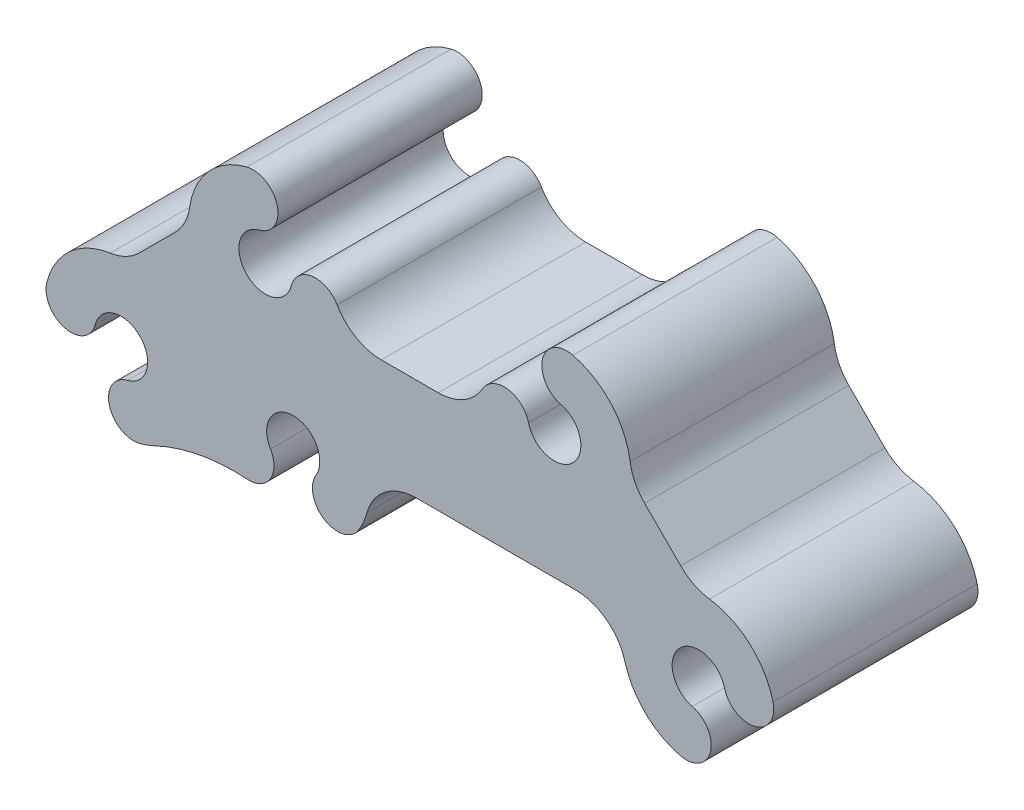
SolidWorks part; units mm, degrees
ref_plane "Front Plane" through (0, 0, 0) normal (0, 0, 1) x (1, 0, 0)
ref_plane "Top Plane" through (0, 0, 0) normal (0, 1, 0) x (1, 0, 0)
ref_plane "Right Plane" through (0, 0, 0) normal (1, 0, 0) x (0, 0, -1)
ref_plane "Plane1" through (0, 0, 0) normal (0, 0, -1) x (-1, 0, 0)
sketch "Sketch1" plane through (0, 0, 0) normal (0, 0, -1) x (-1, 0, 0)
  line L0 (-28.4032, 13.6299) -> (-32.8933, 9.1398)
  line L1 (-19.8469, 0) -> (0, 0)
  line L2 (34.4586, 9.1398) -> (29.9685, 13.6299)
  line L3 (4.3259, 12.7) -> (-2.7576, 12.7)
  arc A0 (-26.6071, 17.222) -> (-28.4032, 13.6299) centre (-32.8933, 18.1201) cw
  arc A1 (-32.8933, 9.1398) -> (-36.4854, 7.3438) centre (-37.3834, 13.6299) cw
  arc A2 (-36.4854, 7.3438) -> (-44.3795, 0.2224) centre (-35.1384, -2.0855) ccw
  arc A3 (-44.3795, 0.2224) -> (-38.342, -1.2854) centre (-41.3607, -0.5315) ccw
  arc A4 (-38.342, -1.2854) -> (-34.3383, -5.2891) centre (-35.1384, -2.0855) cw
  arc A5 (-34.3383, -5.2891) -> (-32.8305, -11.3267) centre (-33.5844, -8.3079) ccw
  arc A6 (-32.8305, -11.3267) -> (-25.9635, -4.6442) centre (-35.1384, -2.0855) ccw
  arc A7 (-25.9635, -4.6442) -> (-19.8469, 0) centre (-19.8469, -6.35) cw
  arc A8 (0, 0) -> (6.1166, -4.6442) centre (0, -6.35) cw
  arc A9 (6.1166, -4.6442) -> (7.1251, -6.9881) centre (15.2915, -2.0855) ccw
  arc A10 (7.1251, -6.9881) -> (12.4605, -3.7851) centre (9.7928, -5.3866) ccw
  arc A11 (12.4605, -3.7851) -> (18.1225, -3.7851) centre (15.2915, -2.0855) cw
  arc A12 (18.1225, -3.7851) -> (21.0041, -8.4907) centre (20.7902, -5.3866) ccw
  arc A13 (21.0041, -8.4907) -> (32.6197, -10.6906) centre (22.6088, -31.7841) cw
  arc A14 (32.6197, -10.6906) -> (34.3958, -11.3267) centre (36.7037, -2.0855) ccw
  arc A15 (34.3958, -11.3267) -> (35.9036, -5.2891) centre (35.1497, -8.3079) ccw
  arc A16 (35.9036, -5.2891) -> (39.9073, -1.2854) centre (36.7037, -2.0855) cw
  arc A17 (39.9073, -1.2854) -> (45.9449, 0.2224) centre (42.9261, -0.5315) ccw
  arc A18 (45.9449, 0.2224) -> (38.0507, 7.3438) centre (36.7037, -2.0855) ccw
  arc A19 (38.0507, 7.3438) -> (34.4586, 9.1398) centre (38.9488, 13.6299) cw
  arc A20 (29.9685, 13.6299) -> (28.1725, 17.222) centre (34.4586, 18.1201) cw
  arc A21 (28.1725, 17.222) -> (21.0511, 25.1162) centre (18.7432, 15.875) ccw
  arc A22 (21.0511, 25.1162) -> (19.5432, 19.0786) centre (20.2972, 22.0974) ccw
  arc A23 (19.5432, 19.0786) -> (15.5396, 15.0749) centre (18.7432, 15.875) cw
  arc A24 (15.5396, 15.0749) -> (9.8258, 15.8762) centre (12.5208, 14.321) ccw
  arc A25 (9.8258, 15.8762) -> (4.3259, 12.7) centre (4.3259, 19.05) cw
  arc A26 (-2.7576, 12.7) -> (-8.2589, 15.8786) centre (-2.7576, 19.05) cw
  arc A27 (-8.2589, 15.8786) -> (-13.9738, 15.0767) centre (-10.9546, 14.3245) ccw
  arc A28 (-13.9738, 15.0767) -> (-17.9797, 19.0782) centre (-17.1778, 15.875) cw
  arc A29 (-17.9797, 19.0782) -> (-19.491, 25.1149) centre (-18.7353, 22.0965) ccw
  arc A30 (-19.491, 25.1149) -> (-26.6071, 17.222) centre (-17.1778, 15.875) ccw
extrude "Extrude1" add sketch "Sketch1" against normal blind 25.4
